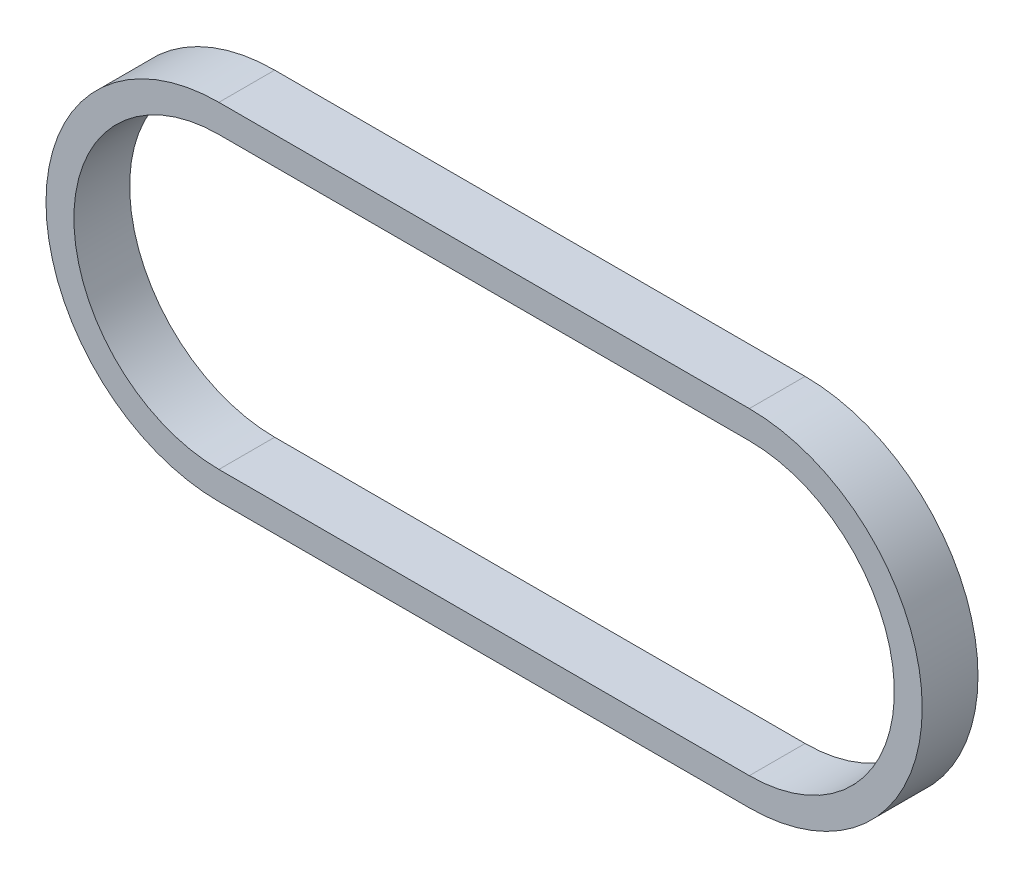
SolidWorks part; units mm, degrees
ref_plane "Front Plane" through (0, 0, 0) normal (0, 0, 1) x (1, 0, 0)
ref_plane "Top Plane" through (0, 0, 0) normal (0, 1, 0) x (1, 0, 0)
ref_plane "Right Plane" through (0, 0, 0) normal (1, 0, 0) x (0, 0, -1)
sketch "Sketch1" plane through (0, 0, 0) normal (0, 0, 1) x (1, 0, 0)
  line L0 (0, 0) -> (95.1, 0) construction
  line L1 (0, 26) -> (95.1, 26)
  line L2 (0, -26) -> (95.1, -26)
  line L3 (0, 31) -> (95.1, 31)
  line L4 (0, -31) -> (95.1, -31)
  arc A0 (0, 26) -> (0, -26) centre (0, 0) ccw
  arc A1 (95.1, -26) -> (95.1, 26) centre (95.1, 0) ccw
  arc A2 (95.1, -31) -> (95.1, 31) centre (95.1, 0) ccw
  arc A3 (0, 31) -> (0, -31) centre (0, 0) ccw
  point P3 (47.55, 0)
  dimension "D1" = 26
  dimension "D2" = 95.1
  dimension "D3" = 5
extrude "Boss-Extrude1" add sketch "Sketch1" along normal blind 10
